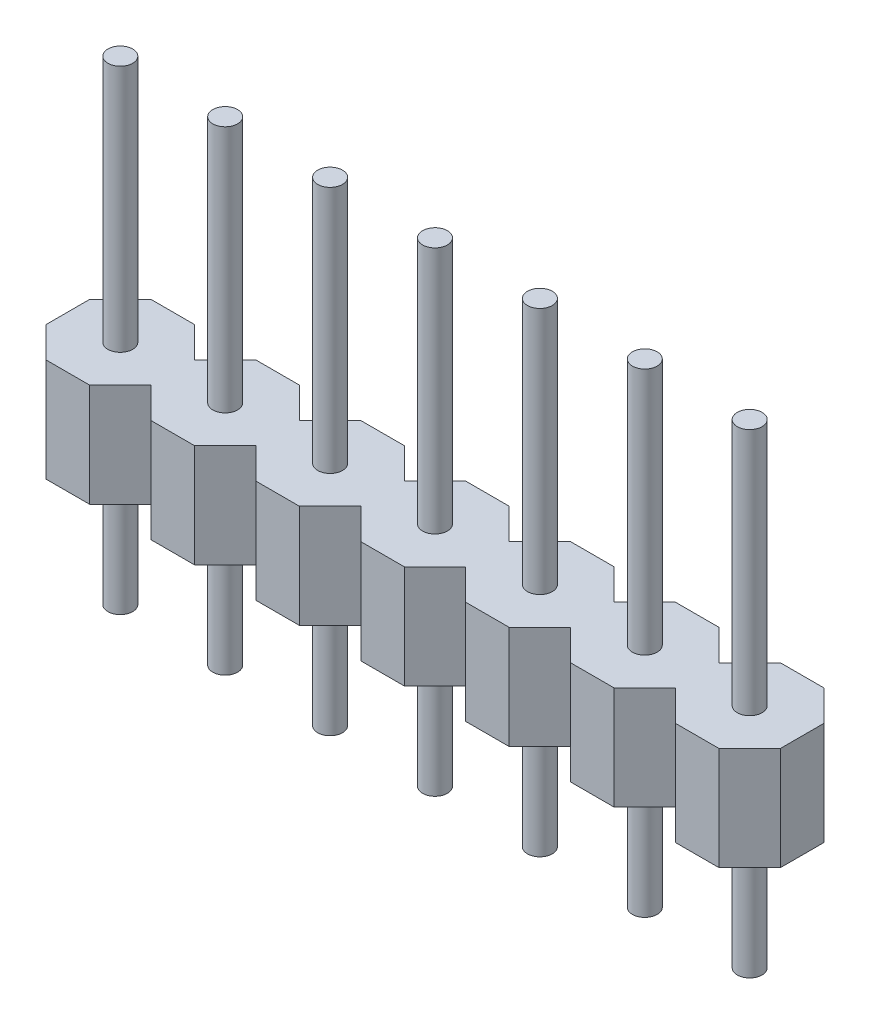
SolidWorks part; units mm, degrees
ref_plane "Спереди" through (0, 0, 0) normal (0, 0, 1) x (1, 0, 0)
ref_plane "Сверху" through (0, 0, 0) normal (0, 1, 0) x (1, 0, 0)
ref_plane "Справа" through (0, 0, 0) normal (1, 0, 0) x (0, 0, -1)
sketch "Эскиз1" plane through (0, 0, 0) normal (0, 1, 0) x (1, 0, 0)
  line L0 (16.51, -0.5261) -> (16.51, 0.5261)
  line L1 (3.81, -0.5261) -> (3.81, 0.5261)
  line L2 (3.81, 0.5261) -> (3.0661, 1.27)
  line L3 (1.27, -0.5261) -> (1.27, 0.5261)
  line L4 (1.27, 0.5261) -> (0.5261, 1.27)
  line L5 (0.5261, 1.27) -> (-0.5261, 1.27)
  line L6 (-0.5261, 1.27) -> (-1.27, 0.5261)
  line L7 (-1.27, 0.5261) -> (-1.27, -0.5261)
  line L8 (-1.27, -0.5261) -> (-0.5261, -1.27)
  line L9 (-0.5261, -1.27) -> (0.5261, -1.27)
  line L10 (0.5261, -1.27) -> (1.27, -0.5261)
  line L11 (3.0661, 1.27) -> (2.0139, 1.27)
  line L12 (2.0139, 1.27) -> (1.27, 0.5261)
  line L13 (1.27, 0.5261) -> (1.27, -0.5261)
  line L14 (1.27, -0.5261) -> (2.0139, -1.27)
  line L15 (2.0139, -1.27) -> (3.0661, -1.27)
  line L16 (3.0661, -1.27) -> (3.81, -0.5261)
  line L17 (6.35, -0.5261) -> (6.35, 0.5261)
  line L18 (6.35, 0.5261) -> (5.6061, 1.27)
  line L19 (5.6061, 1.27) -> (4.5539, 1.27)
  line L20 (4.5539, 1.27) -> (3.81, 0.5261)
  line L21 (3.81, 0.5261) -> (3.81, -0.5261)
  line L22 (3.81, -0.5261) -> (4.5539, -1.27)
  line L23 (4.5539, -1.27) -> (5.6061, -1.27)
  line L24 (5.6061, -1.27) -> (6.35, -0.5261)
  line L25 (8.89, -0.5261) -> (8.89, 0.5261)
  line L26 (8.89, 0.5261) -> (8.1461, 1.27)
  line L27 (8.1461, 1.27) -> (7.0939, 1.27)
  line L28 (7.0939, 1.27) -> (6.35, 0.5261)
  line L29 (6.35, 0.5261) -> (6.35, -0.5261)
  line L30 (6.35, -0.5261) -> (7.0939, -1.27)
  line L31 (7.0939, -1.27) -> (8.1461, -1.27)
  line L32 (8.1461, -1.27) -> (8.89, -0.5261)
  line L33 (11.43, -0.5261) -> (11.43, 0.5261)
  line L34 (11.43, 0.5261) -> (10.6861, 1.27)
  line L35 (10.6861, 1.27) -> (9.6339, 1.27)
  line L36 (9.6339, 1.27) -> (8.89, 0.5261)
  line L37 (8.89, 0.5261) -> (8.89, -0.5261)
  line L38 (8.89, -0.5261) -> (9.6339, -1.27)
  line L39 (9.6339, -1.27) -> (10.6861, -1.27)
  line L40 (10.6861, -1.27) -> (11.43, -0.5261)
  line L41 (13.97, -0.5261) -> (13.97, 0.5261)
  line L42 (13.97, 0.5261) -> (13.2261, 1.27)
  line L43 (13.2261, 1.27) -> (12.1739, 1.27)
  line L44 (12.1739, 1.27) -> (11.43, 0.5261)
  line L45 (11.43, 0.5261) -> (11.43, -0.5261)
  line L46 (11.43, -0.5261) -> (12.1739, -1.27)
  line L47 (12.1739, -1.27) -> (13.2261, -1.27)
  line L48 (13.2261, -1.27) -> (13.97, -0.5261)
  line L49 (16.51, 0.5261) -> (15.7661, 1.27)
  line L50 (15.7661, 1.27) -> (14.7139, 1.27)
  line L51 (14.7139, 1.27) -> (13.97, 0.5261)
  line L52 (13.97, 0.5261) -> (13.97, -0.5261)
  line L53 (13.97, -0.5261) -> (14.7139, -1.27)
  line L54 (14.7139, -1.27) -> (15.7661, -1.27)
  line L55 (15.7661, -1.27) -> (16.51, -0.5261)
  circle A0 centre (15.24, 0) radius 1.27 construction
  circle A6 centre (0, 0) radius 1.27 construction
  circle A7 centre (2.54, 0) radius 1.27 construction
  circle A8 centre (5.08, 0) radius 1.27 construction
  circle A9 centre (7.62, 0) radius 1.27 construction
  circle A10 centre (10.16, 0) radius 1.27 construction
  circle A11 centre (12.7, 0) radius 1.27 construction
  dimension "D1" = 7
extrude "Бобышка-Вытянуть1" add sketch "Эскиз1" along normal blind 2.5 contours L9 L10 L3 L4 L5 L6 L7 L8 | L15 L16 L1 L2 L11 L12 L3 L14 | L31 L32 L25 L26 L27 L28 L17 L30 | L39 L40 L33 L34 L35 L36 L25 L38 | L47 L48 L41 L42 L43 L44 L33 L46 | L54 L55 L0 L49 L50 L51 L41 L53
sketch "Эскиз2" plane through (0, 2.5, 0) normal (0, 1, 0) x (1, 0, 0)
  circle A0 centre (0, 0) radius 0.3
  circle A1 centre (2.54, 0) radius 0.3
  circle A2 centre (5.08, 0) radius 0.3
  circle A3 centre (7.62, 0) radius 0.3
  circle A4 centre (10.16, 0) radius 0.3
  circle A5 centre (12.7, 0) radius 0.3
  circle A6 centre (15.24, 0) radius 0.3
  dimension "D1" = 7
extrude "Бобышка-Вытянуть2" add sketch "Эскиз2" along normal blind 6
sketch "Эскиз3" plane through (0, 0, 0) normal (0, -1, 0) x (1, 0, 0)
  circle A0 centre (0, 0) radius 0.3
  circle A1 centre (2.54, 0) radius 0.3
  circle A2 centre (5.08, 0) radius 0.3
  circle A3 centre (7.62, 0) radius 0.3
  circle A4 centre (10.16, 0) radius 0.3
  circle A5 centre (12.7, 0) radius 0.3
  circle A6 centre (15.24, 0) radius 0.3
  dimension "D1" = 7
extrude "Бобышка-Вытянуть3" add sketch "Эскиз3" along normal blind 3
